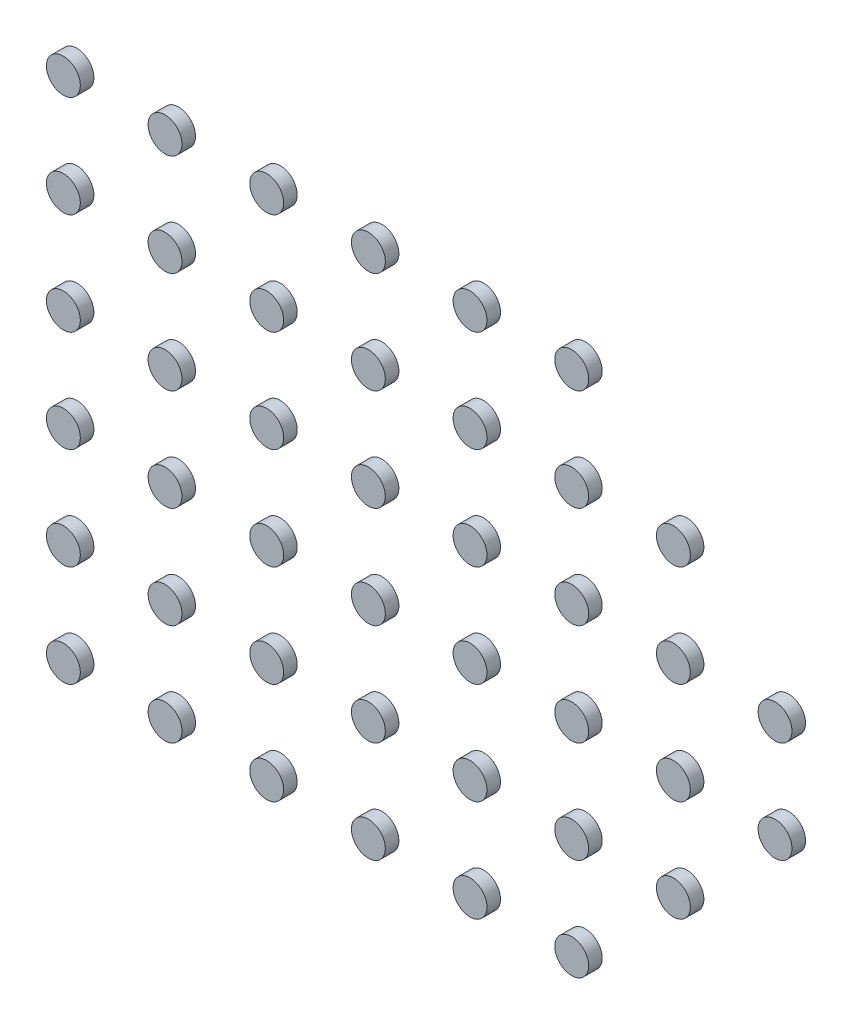
SolidWorks part; units mm, degrees
ref_plane "前视基准面" through (0, 0, 0) normal (0, 0, 1) x (1, 0, 0)
ref_plane "上视基准面" through (0, 0, 0) normal (0, 1, 0) x (1, 0, 0)
ref_plane "右视基准面" through (0, 0, 0) normal (1, 0, 0) x (0, 0, -1)
other "Configuration Table"
sketch "草图1" plane through (0, 0, 0) normal (0, 0, 1) x (1, 0, 0)
  circle A0 centre (-10.5, -7.5) radius 0.5
  circle A1 centre (-10.5, -4.5) radius 0.5
  circle A2 centre (-10.5, -1.5) radius 0.5
  circle A3 centre (-10.5, 4.5) radius 0.5
  circle A4 centre (-7.5, 4.5) radius 0.5
  circle A5 centre (-7.5, -1.5) radius 0.5
  circle A6 centre (-7.5, -4.5) radius 0.5
  circle A7 centre (-7.5, -7.5) radius 0.5
  circle A8 centre (-4.5, -7.5) radius 0.5
  circle A9 centre (-4.5, -4.5) radius 0.5
  circle A10 centre (-4.5, 1.5) radius 0.5
  circle A11 centre (-4.5, 4.5) radius 0.5
  circle A12 centre (-1.5, 4.5) radius 0.5
  circle A13 centre (-1.5, 1.5) radius 0.5
  circle A14 centre (1.5, -1.5) radius 0.5
  circle A15 centre (-1.5, -1.5) radius 0.5
  circle A16 centre (-1.5, -4.5) radius 0.5
  circle A17 centre (-1.5, -7.5) radius 0.5
  circle A18 centre (1.5, -7.5) radius 0.5
  circle A19 centre (1.5, -4.5) radius 0.5
  circle A20 centre (1.5, 1.5) radius 0.5
  circle A21 centre (1.5, 4.5) radius 0.5
  circle A22 centre (4.5, 4.5) radius 0.5
  circle A23 centre (4.5, 1.5) radius 0.5
  circle A24 centre (4.5, -1.5) radius 0.5
  circle A25 centre (4.5, -4.5) radius 0.5
  circle A26 centre (4.5, -7.5) radius 0.5
  circle A27 centre (7.5, -4.5) radius 0.5
  circle A28 centre (7.5, 1.5) radius 0.5
  circle A29 centre (7.5, -1.5) radius 0.5
  circle A30 centre (10.5, -1.5) radius 0.5
  circle A31 centre (10.5, 1.5) radius 0.5
  circle A32 centre (7.5, 4.5) radius 0.5
  circle A33 centre (4.5, 7.5) radius 0.5
  circle A34 centre (1.5, 7.5) radius 0.5
  circle A35 centre (-1.5, 7.5) radius 0.5
  circle A36 centre (-4.5, 7.5) radius 0.5
  circle A37 centre (-7.5, 7.5) radius 0.5
  circle A38 centre (-10.5, 7.5) radius 0.5
  circle A39 centre (-4.5, -1.5) radius 0.5
  circle A40 centre (-1.5, -1.5) radius 0.5
  circle A41 centre (-7.5, 1.5) radius 0.5
  circle A42 centre (-10.5, 1.5) radius 0.5
  point P86 (0, 0)
  point P87 (0, 0)
extrude "凸台-拉伸1" add sketch "草图1" along normal blind 0.4 contours A10 | A13 | A20 | A23 | A28 | A31 | A30 | A29 | A38 | A35 | A34 | A33 | A42 | A3 | A2 | A1 | A0 | A7 | A6 | A5 | A41 | A4 | A11 | A12 | A21 | A32 | A14 | A15 | A39 | A9 | A16 | A8 | A17 | A18 | A26 | A25 | A27 | A24 | A37 | A36 | A22 | A19
